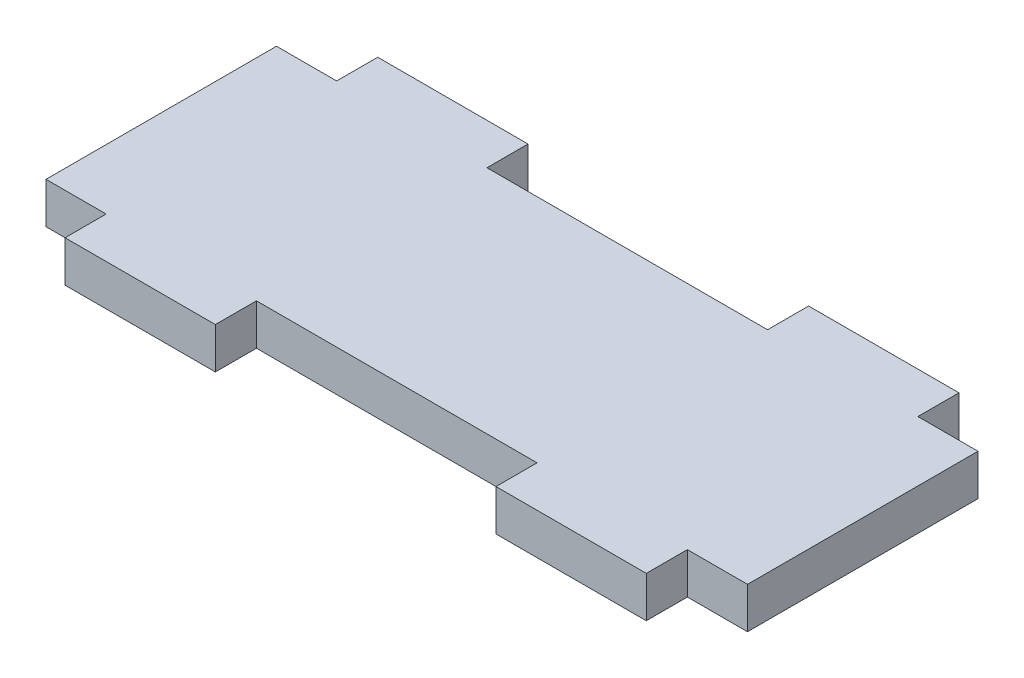
SolidWorks part; units mm, degrees
material "Corrugated Paper"
ref_plane "Front Plane" through (0, 0, 0) normal (0, 0, 1) x (1, 0, 0)
ref_plane "Top Plane" through (0, 0, 0) normal (0, 1, 0) x (1, 0, 0)
ref_plane "Right Plane" through (0, 0, 0) normal (1, 0, 0) x (0, 0, -1)
sketch "Sketch1" plane through (0, 0, 0) normal (0, 1, 0) x (1, 0, 0)
  line L0 (35, 23) -> (35, 0) construction
  line L1 (0, 0) -> (70, 0) construction
  line L2 (0, 0) -> (0, 23)
  line L3 (0, 23) -> (70, 23) construction
  line L4 (70, 0) -> (70, 23)
  line L5 (6, 23) -> (0, 23)
  line L6 (64, 23) -> (70, 23)
  line L7 (6, 23) -> (6, 27.1)
  line L8 (6, 27.1) -> (21, 27.1)
  line L9 (21, 23) -> (21, 27.1)
  line L10 (21, 23) -> (49, 23)
  line L11 (64, 27.1) -> (49, 27.1)
  line L12 (49, 27.1) -> (49, 23)
  line L13 (64, 27.1) -> (64, 23)
  line L14 (0, 11.5) -> (70, 11.5) construction
  line L15 (0, 0) -> (70, 0) construction
  line L16 (64, -4.1) -> (64, 0)
  line L17 (49, -4.1) -> (49, 0)
  line L18 (64, -4.1) -> (49, -4.1)
  line L19 (21, 0) -> (49, 0)
  line L20 (21, 0) -> (21, -4.1)
  line L21 (6, -4.1) -> (21, -4.1)
  line L22 (6, 0) -> (6, -4.1)
  line L23 (64, 0) -> (70, 0)
  line L24 (6, 0) -> (0, 0)
  dimension "D1" = 23
  dimension "D2" = 70
  dimension "D3" = 28
  dimension "D4" = 15
  dimension "D5" = 4.1
extrude "Boss-Extrude1" add sketch "Sketch1" along normal blind 4.1
